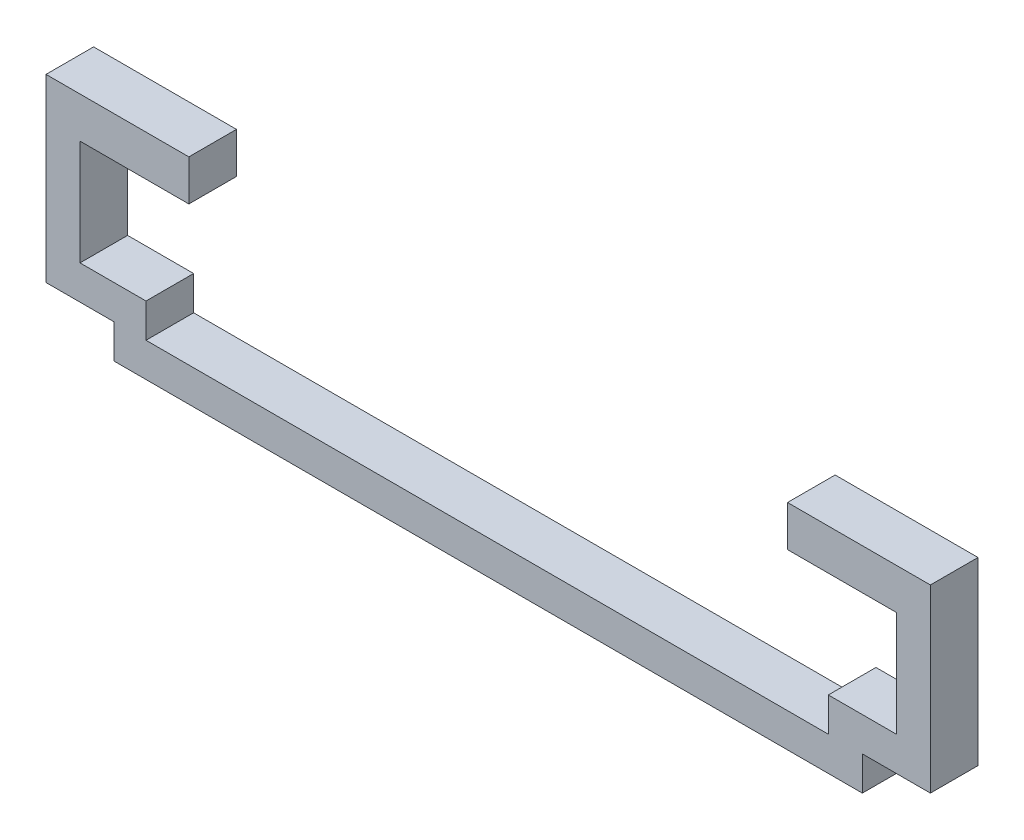
SolidWorks part; units mm, degrees
ref_plane "前视基准面" through (0, 0, 0) normal (0, 0, 1) x (1, 0, 0)
ref_plane "上视基准面" through (0, 0, 0) normal (0, 1, 0) x (1, 0, 0)
ref_plane "右视基准面" through (0, 0, 0) normal (1, 0, 0) x (0, 0, -1)
sketch "草图1" plane through (0, 0, 0) normal (0, 0, 1) x (1, 0, 0)
  line L1 (-50, 2.5) -> (50, 2.5)
  line L2 (-50, 2.5) -> (-50, -2.5)
  line L3 (-50, -2.5) -> (50, -2.5)
  line L4 (50, 2.5) -> (50, -2.5)
  line L5 (-50, 2.5) -> (50, -2.5) construction
  line L6 (-50, -2.5) -> (50, 2.5) construction
  point P0 (0, 0)
  dimension "D1" = 100
  dimension "D2" = 5
extrude "凸台-拉伸1" add sketch "草图1" along normal blind 8.8
sketch "草图2" plane through (0, 0, 0) normal (0, 0, -1) x (-1, 0, 0)
  line L1 (-50, -2.5) -> (-55, -2.5)
  line L2 (-50, -2.5) -> (-50, 7.5)
  line L3 (-50, 7.5) -> (-55, 7.5)
  line L4 (-55, -2.5) -> (-55, 7.5)
  dimension "D1" = 5
  dimension "D2" = 10
extrude "凸台-拉伸2" add sketch "草图2" against normal blind 8.8
sketch "草图3" plane through (0, 0, 0) normal (0, 0, -1) x (-1, 0, 0)
  line L1 (50, -2.5) -> (55, -2.5)
  line L2 (50, -2.5) -> (50, 7.5)
  line L3 (50, 7.5) -> (55, 7.5)
  line L4 (55, -2.5) -> (55, 7.5)
  dimension "D1" = 5
  dimension "D2" = 10
extrude "凸台-拉伸3" add sketch "草图3" against normal blind 8.8
sketch "草图4" plane through (0, 0, 8.8) normal (0, 0, 1) x (1, 0, 0)
  line L2 (-55, 7.5) -> (-60, 7.5)
  line L3 (-55, 7.5) -> (-55, 2.5)
  line L4 (-55, 2.5) -> (-60, 2.5)
  line L5 (-60, 7.5) -> (-60, 2.5)
  dimension "D1" = 5
  dimension "D2" = 5
extrude "凸台-拉伸4" add sketch "草图4" against normal blind 8.8
sketch "草图5" plane through (0, 0, 8.8) normal (0, 0, 1) x (1, 0, 0)
  line L1 (55, 7.5) -> (60, 7.5)
  line L2 (55, 7.5) -> (55, 2.5)
  line L3 (55, 2.5) -> (60, 2.5)
  line L4 (60, 7.5) -> (60, 2.5)
  dimension "D1" = 5
  dimension "D2" = 5
extrude "凸台-拉伸5" add sketch "草图5" against normal blind 8.8
sketch "草图6" plane through (0, 0, 8.8) normal (0, 0, 1) x (1, 0, 0)
  line L1 (-50, 7.5) -> (-50.3, 7.5)
  line L2 (-50, 7.5) -> (-50, 2.5)
  line L3 (-50, 2.5) -> (-50.3, 2.5)
  line L4 (-50.3, 7.5) -> (-50.3, 2.5)
  dimension "D1" = 0.3
extrude "切除-拉伸1" cut sketch "草图6" against normal blind 8.8
sketch "草图7" plane through (0, 0, 8.8) normal (0, 0, 1) x (1, 0, 0)
  line L1 (-60, 2.5) -> (-65, 2.5)
  line L2 (-60, 2.5) -> (-60, 23)
  line L3 (-60, 23) -> (-65, 23)
  line L4 (-65, 2.5) -> (-65, 23)
  dimension "D1" = 20.5
  dimension "D2" = 5
extrude "凸台-拉伸6" add sketch "草图7" against normal blind 8.8
sketch "草图8" plane through (0, 0, 8.8) normal (0, 0, 1) x (1, 0, 0)
  line L1 (60, 2.5) -> (65, 2.5)
  line L2 (60, 2.5) -> (60, 23)
  line L3 (60, 23) -> (65, 23)
  line L4 (65, 2.5) -> (65, 23)
  dimension "D1" = 5
  dimension "D2" = 20.5
extrude "凸台-拉伸7" add sketch "草图8" against normal blind 8.8
sketch "草图9" plane through (0, 0, 8.8) normal (0, 0, 1) x (1, 0, 0)
  line L1 (-65, 23) -> (-50, 23)
  line L2 (-65, 23) -> (-65, 29)
  line L3 (-65, 29) -> (-50, 29)
  line L4 (-50, 23) -> (-50, 29)
  dimension "D1" = 15
  dimension "D2" = 6
extrude "凸台-拉伸8" add sketch "草图9" against normal blind 8.8
sketch "草图10" plane through (0, 0, 8.8) normal (0, 0, 1) x (1, 0, 0)
  line L0 (65, 2.5) -> (65, 23) construction
  line L1 (65, 23) -> (50, 23)
  line L2 (65, 23) -> (65, 29)
  line L3 (65, 29) -> (50, 29)
  line L4 (50, 23) -> (50, 29)
  line L5 (65, 23) -> (60, 23) construction
  dimension "D1" = 15
  dimension "D2" = 6
extrude "凸台-拉伸9" add sketch "草图10" against normal blind 8.8
sketch "草图11" plane through (0, 0, 8.8) normal (0, 0, 1) x (1, 0, 0)
  line L1 (-50, 23) -> (-51.5, 23)
  line L2 (-50, 23) -> (-50, 21.5)
  line L3 (-50, 21.5) -> (-51.5, 21.5)
  line L4 (-51.5, 23) -> (-51.5, 21.5)
  dimension "D1" = 1.5
  dimension "D2" = 1.5
extrude "凸台-拉伸10" add sketch "草图11" against normal blind 8.8
sketch "草图12" plane through (0, 0, 8.8) normal (0, 0, 1) x (1, 0, 0)
  line L1 (50, 23) -> (51.5, 23)
  line L2 (50, 23) -> (50, 21.5)
  line L3 (50, 21.5) -> (51.5, 21.5)
  line L4 (51.5, 23) -> (51.5, 21.5)
  dimension "D1" = 1.5
  dimension "D2" = 1.5
extrude "凸台-拉伸11" add sketch "草图12" against normal blind 8.8
sketch "草图14" plane through (0, 0, 8.8) normal (0, 0, 1) x (1, 0, 0)
  line L0 (-51.5, 23) -> (-51.5, 21.5)
  line L1 (-51.5, 21.5) -> (-50, 21.5)
  line L2 (-50, 21.5) -> (-50, 29)
  line L3 (-50, 29) -> (-65, 29)
  line L4 (-65, 29) -> (-65, 2.5)
  line L5 (-65, 2.5) -> (-55, 2.5)
  line L6 (-55, 2.5) -> (-55, -2.5)
  line L7 (-55, -2.5) -> (55, -2.5)
  line L8 (55, -2.5) -> (55, 2.5)
  line L9 (55, 2.5) -> (65, 2.5)
  line L10 (65, 2.5) -> (65, 29)
  line L11 (65, 29) -> (50, 29)
  line L12 (50, 29) -> (50, 21.5)
  line L13 (50, 21.5) -> (51.5, 21.5)
  line L14 (51.5, 21.5) -> (51.5, 23)
  line L15 (51.5, 23) -> (60, 23)
  line L16 (60, 23) -> (60, 7.5)
  line L17 (60, 7.5) -> (50, 7.5)
  line L18 (50, 7.5) -> (50, 2.5)
  line L19 (50, 2.5) -> (-50.3, 2.5)
  line L20 (-50.3, 2.5) -> (-50.3, 7.5)
  line L21 (-50.3, 7.5) -> (-60, 7.5)
  line L22 (-60, 7.5) -> (-60, 23)
  line L23 (-60, 23) -> (-51.5, 23)
extrude "切除-拉伸2" cut sketch "草图14" against normal blind 1.8
sketch "草图15" plane through (0, 0, 7) normal (0, 0, 1) x (1, 0, 0)
  line L1 (-50, 21.5) -> (-51.5, 21.5)
  line L2 (-50, 21.5) -> (-50, 23)
  line L3 (-50, 23) -> (-51.5, 23)
  line L4 (-51.5, 21.5) -> (-51.5, 23)
extrude "切除-拉伸3" cut sketch "草图15" against normal blind 10
sketch "草图16" plane through (0, 0, 7) normal (0, 0, 1) x (1, 0, 0)
  line L1 (50, 21.5) -> (51.5, 21.5)
  line L2 (50, 21.5) -> (50, 23)
  line L3 (50, 23) -> (51.5, 23)
  line L4 (51.5, 21.5) -> (51.5, 23)
extrude "切除-拉伸4" cut sketch "草图16" against normal blind 10
sketch "草图17" plane through (-50, 0, 0) normal (1, 0, 0) x (0, 0, -1)
  line L1 (-7, 29) -> (0, 29)
  line L2 (-7, 29) -> (-7, 23)
  line L3 (-7, 23) -> (0, 23)
  line L4 (0, 29) -> (0, 23)
extrude "凸台-拉伸12" add sketch "草图17" along normal blind 5
sketch "草图18" plane through (50, 0, 0) normal (-1, 0, 0) x (0, 0, 1)
  line L1 (7, 29) -> (0, 29)
  line L2 (7, 29) -> (7, 23)
  line L3 (7, 23) -> (0, 23)
  line L4 (0, 29) -> (0, 23)
extrude "凸台-拉伸13" add sketch "草图18" along normal blind 5
sketch "草图19" plane through (-45, 0, 0) normal (1, 0, 0) x (0, 0, -1)
  line L1 (-7, 29) -> (0, 29)
  line L2 (-7, 29) -> (-7, 23)
  line L3 (-7, 23) -> (0, 23)
  line L4 (0, 29) -> (0, 23)
extrude "凸台-拉伸14" add sketch "草图19" along normal blind 1
sketch "草图20" plane through (45, 0, 0) normal (-1, 0, 0) x (0, 0, 1)
  line L1 (7, 29) -> (0, 29)
  line L2 (7, 29) -> (7, 23)
  line L3 (7, 23) -> (0, 23)
  line L4 (0, 29) -> (0, 23)
extrude "凸台-拉伸15" add sketch "草图20" along normal blind 1
